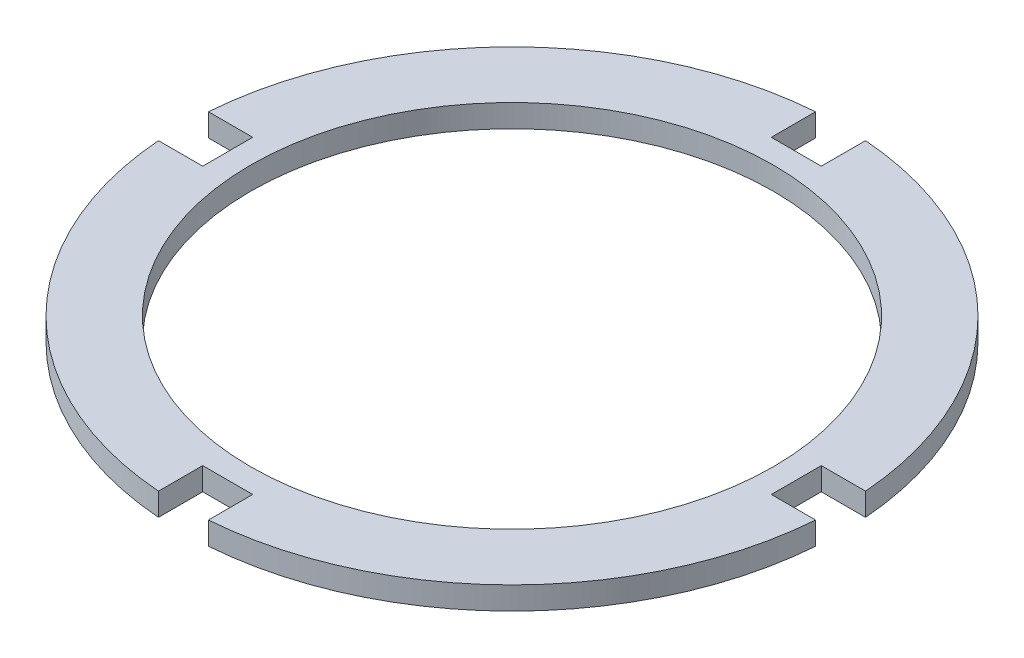
SolidWorks part; units mm, degrees
ref_plane "Front Plane" through (0, 0, 0) normal (0, 0, 1) x (1, 0, 0)
ref_plane "Top Plane" through (0, 0, 0) normal (0, 1, 0) x (1, 0, 0)
ref_plane "Right Plane" through (0, 0, 0) normal (1, 0, 0) x (0, 0, -1)
sketch "Sketch1" plane through (0, 0, 0) normal (0, 1, 0) x (1, 0, 0)
  line L0 (0, 0) -> (0, 171.704) construction
  line L1 (0, 171.704) -> (0, -173.6541) construction
  line L2 (0, 0) -> (168.3436, 0) construction
  line L3 (168.3436, 0) -> (-193.7055, 0) construction
  line L4 (92.263, 6.985) -> (79.441, 6.985)
  line L5 (-6.985, 92.263) -> (6.985, 92.263)
  line L6 (-6.985, 92.263) -> (-6.985, 79.441)
  line L7 (-6.985, 79.441) -> (6.985, 79.441)
  line L8 (6.985, 92.263) -> (6.985, 79.441)
  line L9 (-6.985, 92.263) -> (6.985, 79.441) construction
  line L10 (-6.985, 79.441) -> (6.985, 92.263) construction
  line L11 (92.263, 6.985) -> (92.263, -6.985)
  line L12 (92.263, -6.985) -> (79.441, -6.985)
  line L13 (79.441, 6.985) -> (79.441, -6.985)
  line L14 (6.985, -92.263) -> (6.985, -79.441)
  line L15 (6.985, -92.263) -> (-6.985, -92.263)
  line L16 (-6.985, -92.263) -> (-6.985, -79.441)
  line L17 (6.985, -79.441) -> (-6.985, -79.441)
  line L18 (-92.263, -6.985) -> (-79.441, -6.985)
  line L19 (-92.263, -6.985) -> (-92.263, 6.985)
  line L20 (-92.263, 6.985) -> (-79.441, 6.985)
  line L21 (-79.441, -6.985) -> (-79.441, 6.985)
  line L22 (0, 85.852) -> (0, 0) construction
  circle A0 centre (0, 0) radius 92.075
  circle A1 centre (0, 0) radius 73.025
  point P4 (0, 85.852)
  point P9 (0, 85.852)
  point P29 (0, 0)
  dimension "D1" = 184.15
  dimension "D2" = 146.05
  dimension "D3" = 13.97
  dimension "D4" = 12.8219
  dimension "D6" = 85.852
  dimension "D5" = 4
extrude "Boss-Extrude1" add sketch "Sketch1" along normal blind 6.35 contours L14 A0 L12 L13 L4 L8 L7 L6 L20 L21 L18 L16 L17 A1
